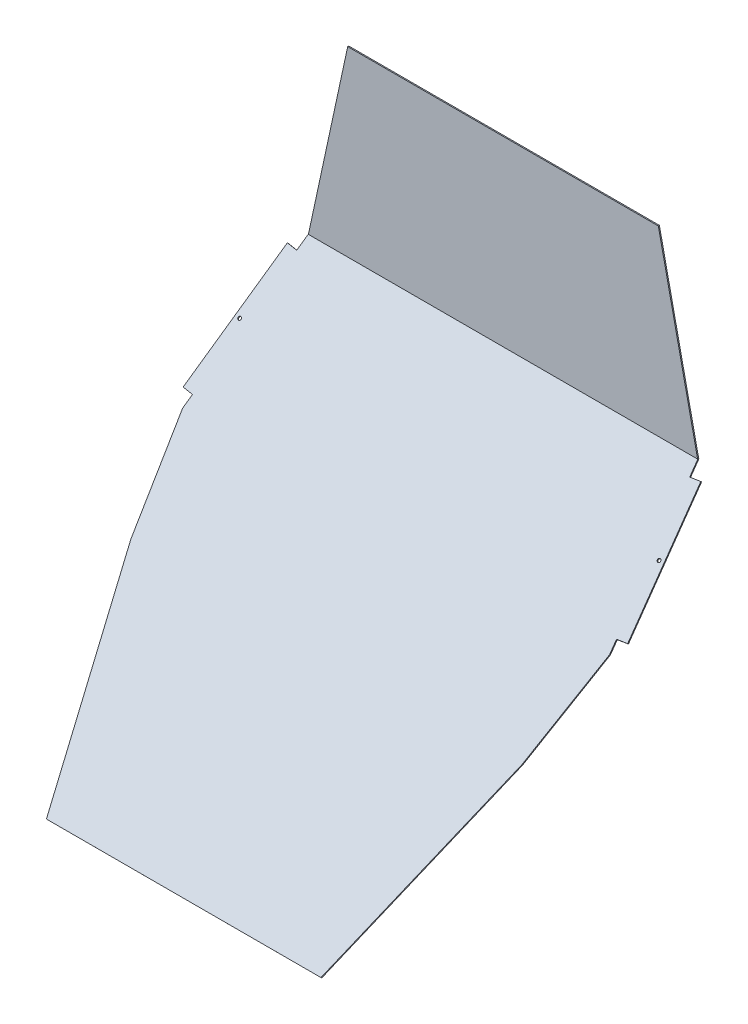
SolidWorks part; units mm, degrees
material "6061 Alloy"
ref_plane "Front Plane" through (0, 0, 0) normal (0, 0, 1) x (1, 0, 0)
ref_plane "Top Plane" through (0, 0, 0) normal (0, 1, 0) x (1, 0, 0)
ref_plane "Right Plane" through (0, 0, 0) normal (1, 0, 0) x (0, 0, -1)
sketch "Sketch1" plane through (0, 0, 0) normal (0, 0, 1) x (1, 0, 0)
  line L0 (-212.5, 0) -> (212.5, 0)
  line L1 (-266.4178, -250) -> (266.4178, -250)
  line L2 (-212.5, 0) -> (-266.4178, -250)
  line L3 (212.5, 0) -> (266.4178, -250)
  line L4 (0, 0) -> (0, -250) construction
  dimension "D1" = 425
  dimension "D2" = 532.8357
  dimension "D3" = 250
extrude "Upper" add sketch "Sketch1" along normal blind 1.5
ref_plane "Seat Angle" through (0, -125.5236, -124.9989) normal (0, 0.7086, 0.7056) x (1, 0, 0)
sketch "Sketch2" plane through (0, -125.5236, -124.9989) normal (0, 0.7086, 0.7056) x (1, 0, 0)
  line L0 (-266.4178, -176.4061) -> (266.4178, -176.4061) construction
  line L1 (-266.4178, -176.4061) -> (266.4178, -176.4061)
  line L2 (-292.1, -383.3919) -> (292.1, -383.3919) construction
  line L3 (0, -176.4061) -> (0, -383.3919) construction
  line L4 (-266.4178, -176.4061) -> (-292.1, -383.3919)
  line L5 (266.4178, -176.4061) -> (292.1, -383.3919)
  line L6 (-267.4432, -518.1752) -> (267.4433, -518.1752) construction
  line L7 (0, -383.3919) -> (0, -518.1752) construction
  line L8 (-292.1, -383.3919) -> (-267.4432, -518.1752)
  line L9 (292.1, -383.3919) -> (267.4433, -518.1752)
  line L10 (-187.8166, -793.663) -> (187.8166, -793.663)
  line L11 (0, -518.1752) -> (0, -793.663) construction
  line L12 (-267.4432, -518.1752) -> (-187.8166, -793.663)
  line L13 (187.8166, -793.663) -> (267.4433, -518.1752)
  line L14 (-279.467, -281.576) -> (-286.9401, -280.6488) construction
  line L15 (-268.8447, -195.9653) -> (-282.8477, -194.2278)
  line L16 (-282.8477, -194.2278) -> (-304.0963, -365.4814)
  line L17 (-304.0963, -365.4814) -> (-290.0933, -367.2189)
  line L18 (268.8447, -195.9653) -> (282.8477, -194.2278)
  line L19 (282.8477, -194.2278) -> (304.0963, -365.4814)
  line L20 (304.0963, -365.4814) -> (290.0933, -367.2189)
  circle A0 centre (-286.9401, -280.6488) radius 2.159
  circle A1 centre (286.9401, -280.6488) radius 2.159
  point P17 (-279.2589, -279.899)
  dimension "D7" = 4.318
  dimension "D8" = 6.58
  dimension "D13" = 7.5304
  dimension "D1" = 584.2
  dimension "D2" = 206.9858
  dimension "D3" = 534.8865
  dimension "D4" = 134.7833
  dimension "D5" = 275.4878
  dimension "D6" = 375.6332
  dimension "D10" = 16.297
  dimension "D11" = 19.7092
  dimension "D12" = 1.6899
extrude "Lower" add sketch "Sketch2" along normal blind 1.5
